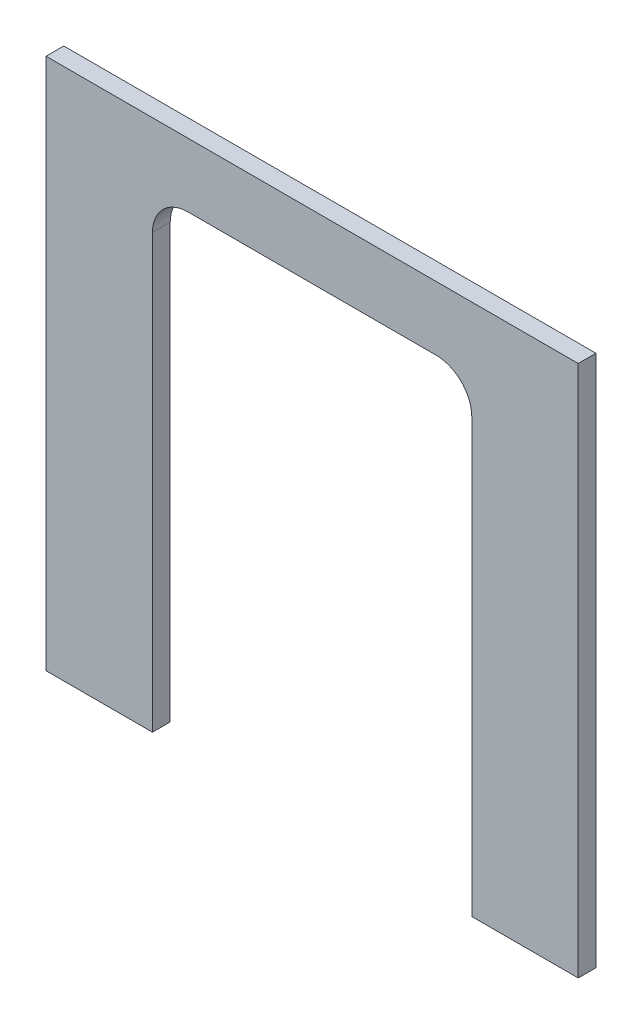
SolidWorks part; units mm, degrees
ref_plane "Front Plane" through (0, 0, 0) normal (0, 0, 1) x (1, 0, 0)
ref_plane "Top Plane" through (0, 0, 0) normal (0, 1, 0) x (1, 0, 0)
ref_plane "Right Plane" through (0, 0, 0) normal (1, 0, 0) x (0, 0, -1)
sketch "Sketch1" plane through (0, 0, 0) normal (0, 0, 1) x (1, 0, 0)
  line L0 (45, -75) -> (45, 47)
  line L1 (-75, 75) -> (75, 75)
  line L2 (-75, 75) -> (-75, -75)
  line L3 (-75, -75) -> (-45, -75)
  line L4 (75, 75) -> (75, -75)
  line L5 (-75, 75) -> (75, -75) construction
  line L6 (-75, -75) -> (75, 75) construction
  line L7 (35, 57) -> (-35, 57)
  line L8 (-45, 47) -> (-45, -75)
  line L9 (45, -75) -> (75, -75)
  arc A0 (45, 47) -> (35, 57) centre (35, 47) ccw
  arc A1 (-35, 57) -> (-45, 47) centre (-35, 47) ccw
  point P0 (0, 0)
  point P8 (0, 0)
  dimension "D3" = 10
  dimension "D6" = 18
  dimension "D1" = 150
  dimension "D2" = 150
  dimension "D4" = 45
  dimension "D5" = 45
extrude "Boss-Extrude1" add sketch "Sketch1" along normal blind 5
